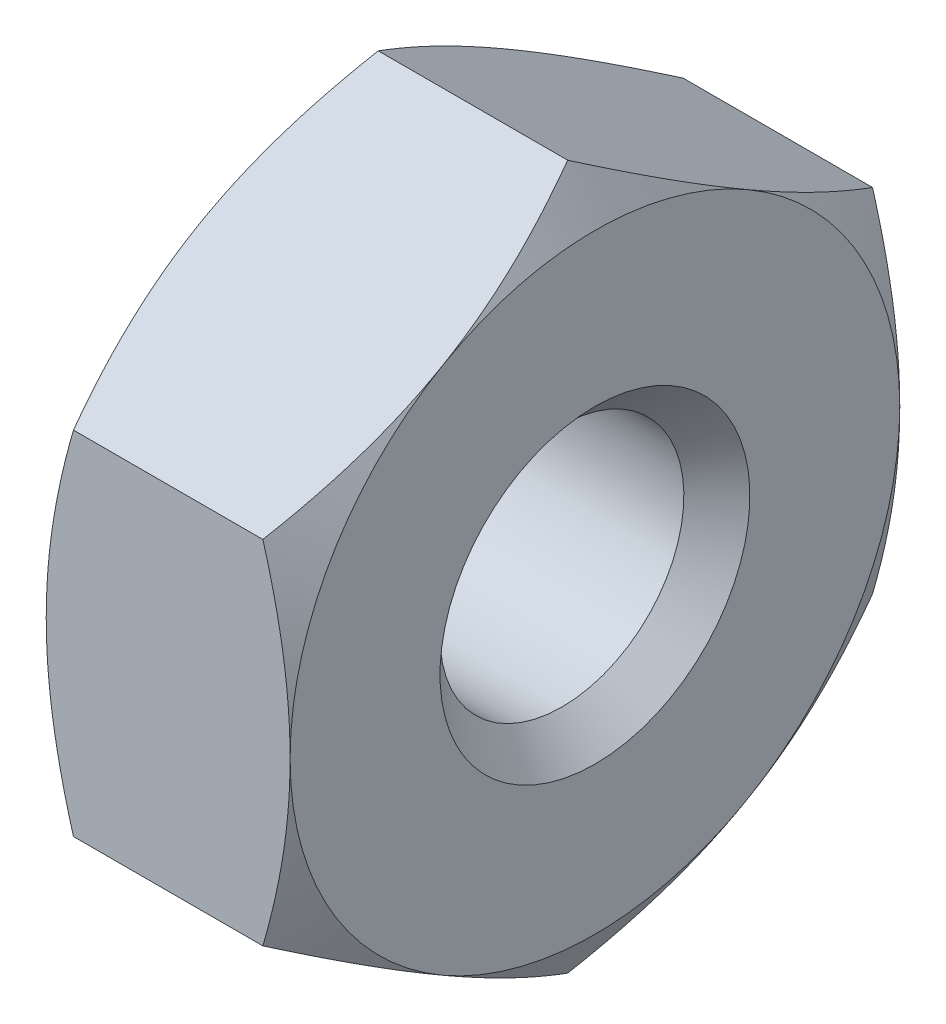
SolidWorks part; units mm, degrees
material "AISI 304"
ref_plane "正面" through (0, 0, 0) normal (0, 0, 1) x (1, 0, 0)
ref_plane "平面" through (0, 0, 0) normal (0, 1, 0) x (1, 0, 0)
ref_plane "右側面" through (0, 0, 0) normal (1, 0, 0) x (0, 0, -1)
ref_plane "Plane1" through (0, 0, 0) normal (0, 0, 1) x (1, 0, 0)
sketch "Sketch1" plane through (0, 0, 0) normal (0, 0, 1) x (1, 0, 0)
  line L0 (0, 0) -> (0, 2)
  line L1 (0, 2) -> (0.2309, 2.4)
  line L2 (0.2309, 2.4) -> (1.3691, 2.4)
  line L3 (1.3691, 2.4) -> (1.6, 2)
  line L4 (1.6, 2) -> (1.6, 0)
  line L5 (1.6, 0) -> (0, 0)
  line L6 (1.6, 0) -> (0, 0) construction
revolve "Revolve1" add sketch "Sketch1" angle 360 about L6
ref_plane "Plane2" through (0, 0, 0) normal (1, 0, 0) x (0, 0, -1)
sketch "Sketch2" plane through (0, 0, 0) normal (1, 0, 0) x (0, 0, -1)
  line L0 (-3, 3) -> (-3, -3)
  line L1 (-3, -3) -> (3, -3)
  line L2 (3, -3) -> (3, 3)
  line L3 (3, 3) -> (-3, 3)
  line L4 (-2, -1.1547) -> (0, -2.3094)
  line L5 (0, -2.3094) -> (2, -1.1547)
  line L6 (2, -1.1547) -> (2, 1.1547)
  line L7 (2, 1.1547) -> (0, 2.3094)
  line L8 (0, 2.3094) -> (-2, 1.1547)
  line L9 (-2, 1.1547) -> (-2, -1.1547)
extrude "Cut-Extrude1" cut sketch "Sketch2" along normal blind 1.6
ref_plane "Plane3" through (0, 0, 0) normal (0, 0, 1) x (1, 0, 0)
sketch "Sketch3" plane through (0, 0, 0) normal (0, 0, 1) x (1, 0, 0)
  line L0 (0, -0.0165) -> (0, 1)
  line L1 (0, 1) -> (0.2165, 0.7835)
  line L2 (0.2165, 0.7835) -> (1.3835, 0.7835)
  line L3 (1.3835, 0.7835) -> (1.6, 1)
  line L4 (1.6, 1) -> (1.6, -0.0165)
  line L5 (1.6, -0.0165) -> (0, -0.0165)
  line L6 (1.6, -0.0165) -> (0, -0.0165) construction
  dimension "D1" = 0.8
revolve "Cut-Revolve1" cut sketch "Sketch3" angle 360 about L6
